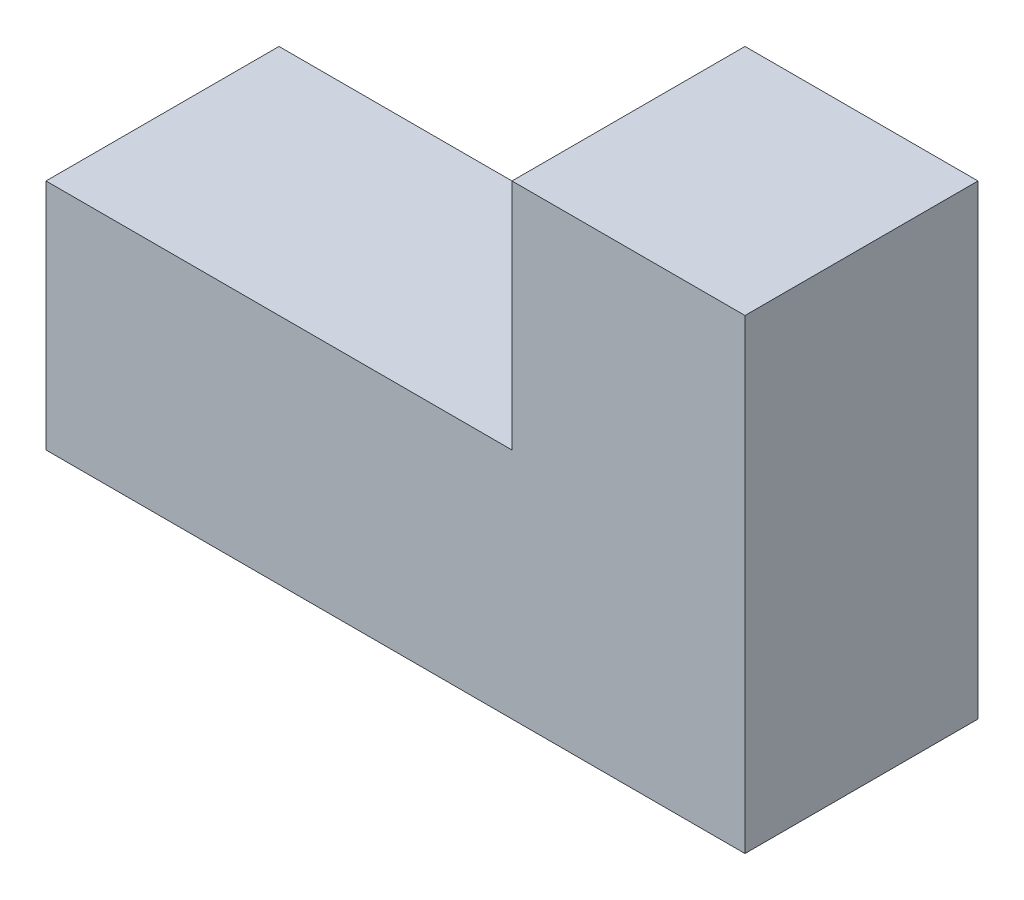
SolidWorks part; units mm, degrees
ref_plane "Front Plane" through (0, 0, 0) normal (0, 0, 1) x (1, 0, 0)
ref_plane "Top Plane" through (0, 0, 0) normal (0, 1, 0) x (1, 0, 0)
ref_plane "Right Plane" through (0, 0, 0) normal (1, 0, 0) x (0, 0, -1)
sketch "Sketch1" plane through (0, 0, 0) normal (0, 0, 1) x (1, 0, 0)
  line L0 (-139.4118, 0) -> (106.7647, 0) construction
  line L1 (0, 72.5) -> (0, -65.4412) construction
  line L2 (-75, 0) -> (15, 0)
  line L3 (15, 0) -> (15, 60)
  line L4 (15, 60) -> (-15, 60)
  line L5 (-15, 60) -> (-15, 30)
  line L6 (-15, 30) -> (-75, 30)
  line L7 (-75, 30) -> (-75, 0)
  dimension "D1" = 30
  dimension "D2" = 90
  dimension "D3" = 60
  dimension "D4" = 60
extrude "Boss-Extrude1" add sketch "Sketch1" against normal blind 30
